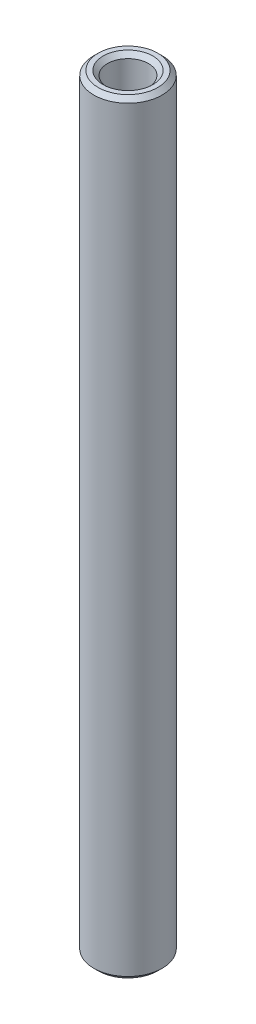
SolidWorks part; units mm, degrees
ref_plane "Front Plane" through (0, 0, 0) normal (0, 0, 1) x (1, 0, 0)
ref_plane "Top Plane" through (0, 0, 0) normal (0, 1, 0) x (1, 0, 0)
ref_plane "Right Plane" through (0, 0, 0) normal (1, 0, 0) x (0, 0, -1)
sketch "Sketch1" plane through (0, 0, 0) normal (0, 1, 0) x (1, 0, 0)
  circle A0 centre (0, 0) radius 1.9844
  circle A1 centre (0, 0) radius 1.1906
  dimension "D1" = 3.9688
  dimension "D2" = 0.7937
extrude "Boss-Extrude1" add sketch "Sketch1" along normal mid plane 44.45
chamfer "Chamfer1" distance 0.254 angle 45 4 edges at (0, -22.225, 1.1906) (0, -22.225, 1.9844) (0, 22.225, 1.1906) (0, 22.225, 1.9844)
